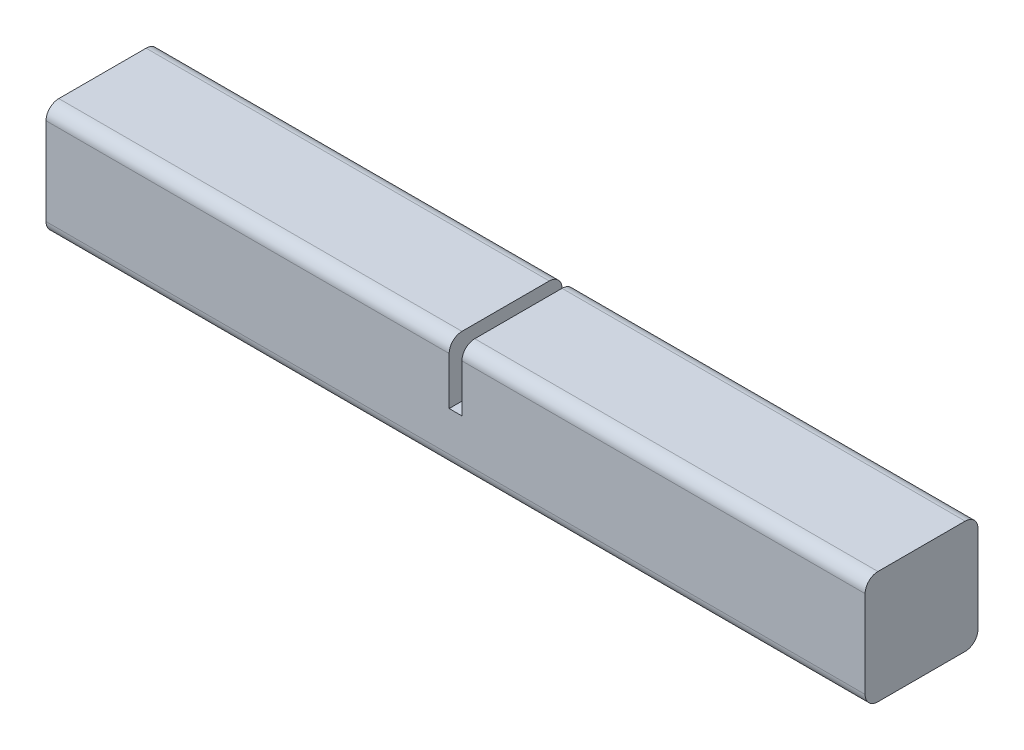
SolidWorks part; units mm, degrees
material "Oak"
ref_plane "Front Plane" through (0, 0, 0) normal (0, 0, 1) x (1, 0, 0)
ref_plane "Top Plane" through (0, 0, 0) normal (0, 1, 0) x (1, 0, 0)
ref_plane "Right Plane" through (0, 0, 0) normal (1, 0, 0) x (0, 0, -1)
sketch "Sketch1" plane through (0, 0, 0) normal (1, 0, 0) x (0, 0, -1)
  line L1 (14, -14) -> (-14, -14)
  line L2 (14, -14) -> (14, 14)
  line L3 (14, 14) -> (-14, 14)
  line L4 (-14, -14) -> (-14, 14)
  line L5 (14, -14) -> (-14, 14) construction
  line L6 (14, 14) -> (-14, -14) construction
  point P0 (0, 0)
  dimension "D1" = 28
  dimension "D2" = 28
extrude "Boss-Extrude1" add sketch "Sketch1" along normal blind 203.2
sketch "Sketch2" plane through (0, 14, 0) normal (0, 1, 0) x (1, 0, 0)
  line L0 (203.2, -14) -> (0, -14) construction
  line L1 (100.0125, 14) -> (103.1875, 14)
  line L2 (100.0125, 14) -> (100.0125, -14)
  line L3 (100.0125, -14) -> (103.1875, -14)
  line L4 (103.1875, 14) -> (103.1875, -14)
  line L5 (203.2, 14) -> (0, 14) construction
  point P6 (101.6, 14)
  dimension "D1" = 3.175
extrude "Cut-Extrude1" cut sketch "Sketch2" against normal blind 15
fillet "Fillet1" radius 3.175 6 edges at (101.6, -14, -14) (101.6, -14, 14) (153.1938, 14, 14) (153.1937, 14, -14) (50.0062, 14, -14) (50.0062, 14, 14)
